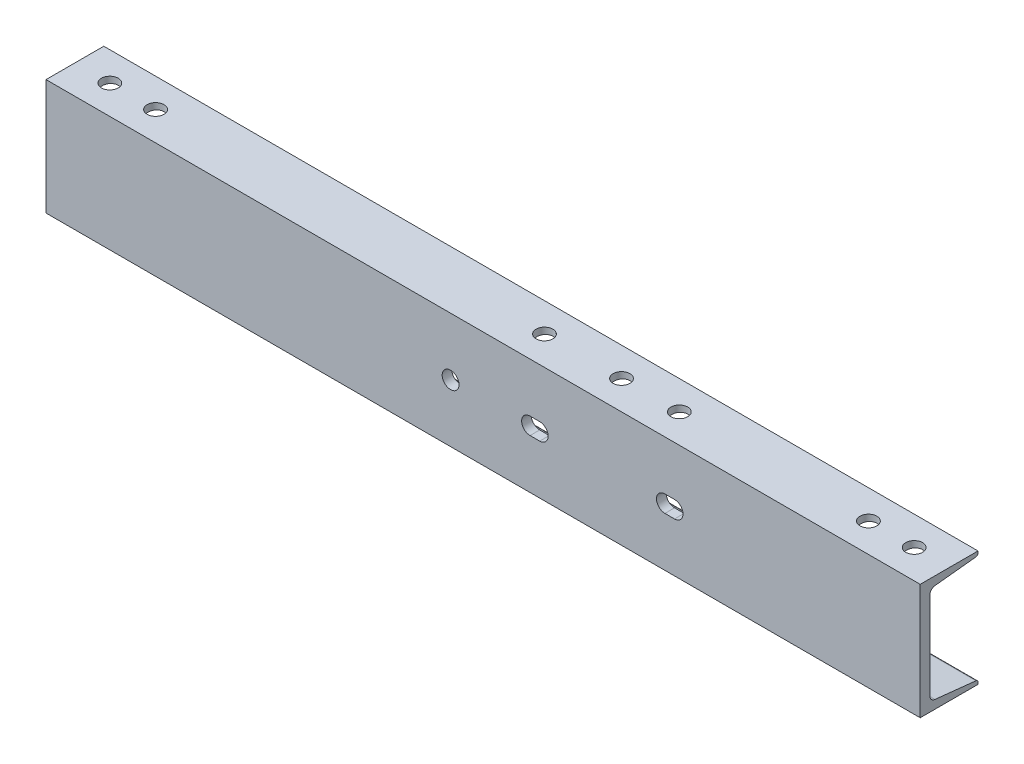
SolidWorks part; units mm, degrees
ref_plane "Front Plane" through (0, 0, 0) normal (0, 0, 1) x (1, 0, 0)
ref_plane "Top Plane" through (0, 0, 0) normal (0, 1, 0) x (1, 0, 0)
ref_plane "Right Plane" through (0, 0, 0) normal (1, 0, 0) x (0, 0, -1)
sketch "Sketch1" plane through (0, 0, 0) normal (1, 0, 0) x (0, 0, -1)
  line L0 (-48.8061, -76.2) -> (-48.8061, 76.2)
  line L1 (-48.8061, 76.2) -> (27.3939, 76.2)
  line L2 (-48.8061, -76.2) -> (27.3939, -76.2)
  line L3 (4.3561, -67.4878) -> (-21.0439, -67.4878) construction
  line L4 (-36.1061, 57.3918) -> (-36.1061, -57.3918)
  line L5 (27.3939, 76.2) -> (27.3939, 73.7107)
  line L6 (27.3939, -76.2) -> (27.3939, -73.7107)
  line L7 (-29.2881, 64.9695) -> (24.6667, 70.6797)
  line L8 (-29.2881, -64.9695) -> (24.6667, -70.6797)
  arc A0 (-36.1061, -57.3918) -> (-29.2881, -64.9695) centre (-28.4861, -57.3918) ccw
  arc A1 (-36.1061, 57.3918) -> (-29.2881, 64.9695) centre (-28.4861, 57.3918) cw
  arc A2 (27.3939, 73.7107) -> (24.6667, 70.6797) centre (24.3459, 73.7107) cw
  arc A3 (27.3939, -73.7107) -> (24.6667, -70.6797) centre (24.3459, -73.7107) ccw
  dimension "D1" = 76.2
  dimension "D2" = 152.4
  dimension "D3" = 12.7
extrude "Boss-Extrude1" add sketch "Sketch1" along normal mid plane 1152.525
sketch "Sketch5" plane through (0, -76.2, 0) normal (0, -1, 0) x (1, 0, 0)
  line L0 (687.9131, 10.7061) -> (42.799, 10.7061) construction
  line L2 (576.2625, 48.8061) -> (576.2625, -27.3939) construction
  line L3 (-576.2625, 48.8061) -> (-576.2625, -27.3939) construction
  line L5 (576.2625, 48.8061) -> (-576.2625, 48.8061) construction
  circle A0 centre (530.225, 10.7061) radius 11.1125
  circle A1 centre (469.9, 10.7061) radius 11.1125
  circle A2 centre (220.599, 10.7061) radius 11.1125
  circle A3 centre (42.799, 10.7061) radius 11.1125
  circle A5 centre (144.399, 10.7061) radius 11.1125
  circle A6 centre (-530.225, 10.7061) radius 11.1125
  circle A7 centre (-469.9, 10.7061) radius 11.1125
  circle A10 centre (84.074, 10.7061) radius 11.1125 [skipped]
  circle A11 centre (160.274, 10.7061) radius 11.1125 [skipped]
  dimension "D2" = 22.225
  dimension "D4" = 60.325
  dimension "D14" = 309.626
  dimension "D15" = 76.2
  dimension "D16" = 22.225
  dimension "D17" = 101.6
  dimension "D3" = 46.0375
  dimension "D10" = 46.0375
  dimension "D11" = 38.1
  dimension "D5" = 2
  dimension "D7" = 2
  dimension "D9" = 2
extrude "Cut-Extrude3" cut sketch "Sketch5" against normal up to surface (152.4 mm away) up to face at (0, 76.2, 10.7061)
sketch "Sketch6" plane through (0, 0, 36.1061) normal (0, 0, -1) x (-1, 0, 0)
  line L0 (576.2625, 0) -> (-576.2625, 0) construction
  line L1 (576.2625, -57.3918) -> (576.2625, 57.3918) construction
  line L3 (-61.9125, 0) -> (-74.6125, 0) construction
  line L4 (-61.9125, -11.1125) -> (-74.6125, -11.1125)
  line L5 (-61.9125, 11.1125) -> (-74.6125, 11.1125)
  line L6 (-239.7125, 0) -> (-252.4125, 0) construction
  line L7 (-239.7125, -11.1125) -> (-252.4125, -11.1125)
  line L8 (-239.7125, 11.1125) -> (-252.4125, 11.1125)
  circle A0 centre (42.8625, 0) radius 11.1125
  arc A1 (-61.9125, -11.1125) -> (-61.9125, 11.1125) centre (-61.9125, 0) ccw
  arc A2 (-74.6125, 11.1125) -> (-74.6125, -11.1125) centre (-74.6125, 0) ccw
  arc A3 (-239.7125, -11.1125) -> (-239.7125, 11.1125) centre (-239.7125, 0) ccw
  arc A4 (-252.4125, 11.1125) -> (-252.4125, -11.1125) centre (-252.4125, 0) ccw
  point P9 (-68.2625, 0)
  point P16 (-246.0625, 0)
  dimension "D1" = 22.225
  dimension "D2" = 533.4
  dimension "D3" = 638.175
  dimension "D5" = 177.8
  dimension "D4" = 12.7
  dimension "D6" = 12.7
extrude "Cut-Extrude4" cut sketch "Sketch6" against normal through all
